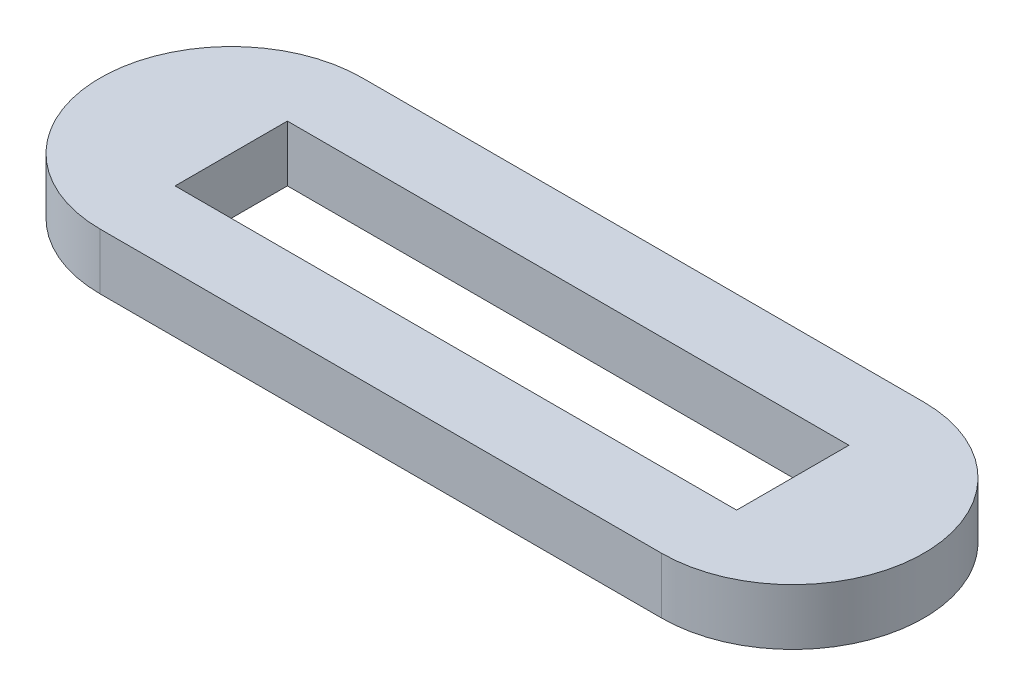
SolidWorks part; units mm, degrees
ref_plane "Alzado" through (0, 0, 0) normal (0, 0, 1) x (1, 0, 0)
ref_plane "Planta" through (0, 0, 0) normal (0, 1, 0) x (1, 0, 0)
ref_plane "Vista lateral" through (0, 0, 0) normal (1, 0, 0) x (0, 0, -1)
sketch "Sketch1" plane through (0, 0, 0) normal (0, 1, 0) x (1, 0, 0)
  line L0 (-75, 0) -> (75, 0) construction
  line L1 (-75, -15) -> (75, -15)
  line L2 (-75, -15) -> (-75, 15)
  line L3 (-75, 15) -> (75, 15)
  line L4 (75, -15) -> (75, 15)
  line L5 (-75, -15) -> (75, 15) construction
  line L6 (-75, 15) -> (75, -15) construction
  line L7 (-75, 35) -> (75, 35)
  line L8 (-75, -35) -> (75, -35)
  arc A0 (-75, 35) -> (-75, -35) centre (-75, 0) ccw
  arc A1 (75, -35) -> (75, 35) centre (75, 0) ccw
  point P0 (0, 0)
  point P8 (0, 0)
  point P13 (0, 0)
  dimension "D3" = 20
  dimension "D1" = 150
  dimension "D2" = 30
extrude "Boss-Extrude1" add sketch "Sketch1" along normal blind 15
